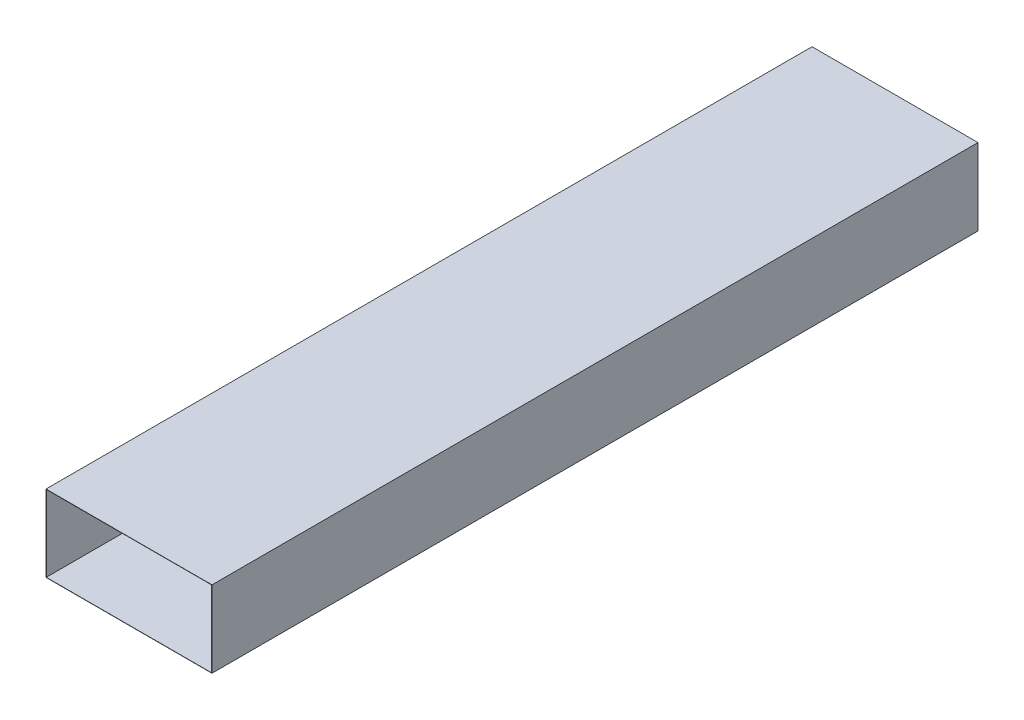
SolidWorks part; units mm, degrees
ref_plane "Front Plane" through (0, 0, 0) normal (0, 0, 1) x (1, 0, 0)
ref_plane "Top Plane" through (0, 0, 0) normal (0, 1, 0) x (1, 0, 0)
ref_plane "Right Plane" through (0, 0, 0) normal (1, 0, 0) x (0, 0, -1)
sketch "Sketch1" plane through (0, 0, 0) normal (0, 0, 1) x (1, 0, 0)
  line L1 (-650, 300) -> (0, 300)
  line L2 (-650, 300) -> (-650, 0)
  line L3 (-650, 0) -> (0, 0)
  line L4 (0, 300) -> (0, 0)
  dimension "D1" = 300
  dimension "D2" = 650
extrude "Extrude-Thin1" add sketch "Sketch1" along normal blind 3000 thin contours L2 L3 L4 L1
